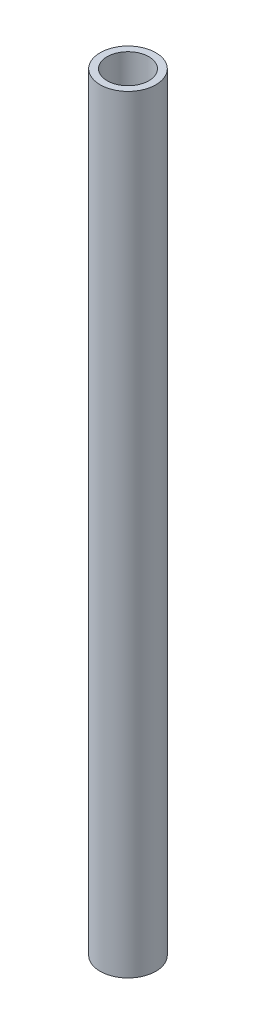
SolidWorks part; units mm, degrees
ref_plane "Front Plane" through (0, 0, 0) normal (0, 0, 1) x (1, 0, 0)
ref_plane "Top Plane" through (0, 0, 0) normal (0, 1, 0) x (1, 0, 0)
ref_plane "Right Plane" through (0, 0, 0) normal (1, 0, 0) x (0, 0, -1)
sketch "Sketch1" plane through (0, 0, 0) normal (0, 1, 0) x (1, 0, 0)
  circle A0 centre (-391.1817, 212.7433) radius 12.7
  circle A1 centre (-391.1817, 212.7433) radius 9.525
  dimension "D1" = 19.05
  dimension "D2" = 25.4
extrude "Boss-Extrude2" add sketch "Sketch1" along normal blind 350.52
